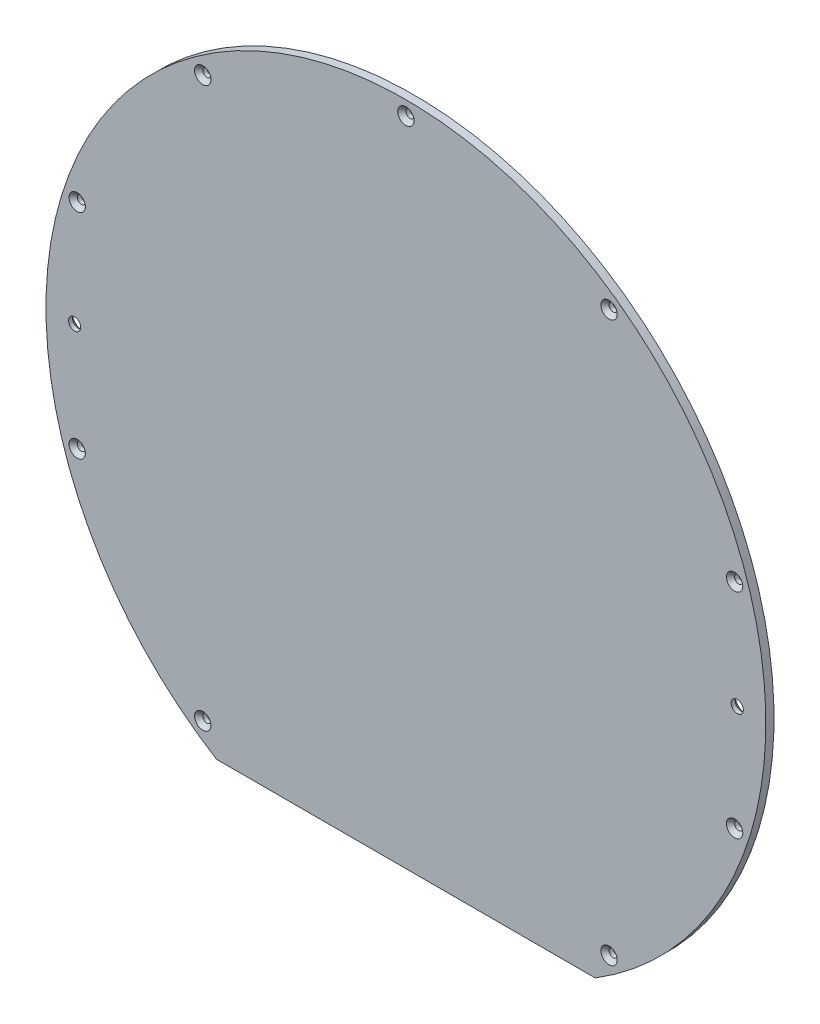
SolidWorks part; units mm, degrees
ref_plane "Plano frontal" through (0, 0, 0) normal (0, 0, 1) x (1, 0, 0)
ref_plane "Plano superior" through (0, 0, 0) normal (0, 1, 0) x (1, 0, 0)
ref_plane "Plano direito" through (0, 0, 0) normal (1, 0, 0) x (0, 0, -1)
sketch "Esboço1" plane through (0, 0, 0) normal (0, 0, 1) x (1, 0, 0)
  line L0 (-46.3033, -74.8331) -> (46.3033, -74.8331)
  line L1 (0, 0) -> (0, -74.8331) construction
  line L2 (-50, -74.8331) -> (50, -74.8331) construction
  arc A0 (46.3033, -74.8331) -> (-46.3033, -74.8331) centre (0, 0) ccw
  arc A1 (50, -74.8331) -> (-50, -74.8331) centre (0, 0) ccw construction
  dimension "D1" = 88
  dimension "D3" = 180
  dimension "D4" = 100
extrude "Ressalto-extrusão1" add sketch "Esboço1" along normal blind 2
sketch "Esboço3" plane through (0, 0, 2) normal (0, 0, 1) x (1, 0, 0)
  line L0 (-81, 0) -> (81, 0) construction
  circle A0 centre (81, 0) radius 1.5
  circle A1 centre (-81, 0) radius 1.5
  dimension "D1" = 3
  dimension "D2" = 162
extrude "Corte-extrusão2" cut sketch "Esboço3" against normal up to next
chamfer "Chanfro2" distance 1 angle 45 2 edges at (82.5, 0, 0) (-79.5, 0, 0)
sketch "Esboço4" plane through (0, 0, 2) normal (0, 0, 1) x (1, 0, 0)
  circle A0 centre (-49.6679, -68.3619) radius 1 construction
  circle A1 centre (-80.3643, -26.1119) radius 1 construction
  circle A2 centre (-80.3643, 26.1119) radius 1 construction
  circle A3 centre (-49.6679, 68.3619) radius 1 construction
  circle A4 centre (0, 84.5) radius 1 construction
  circle A5 centre (49.6679, 68.3619) radius 1 construction
  circle A6 centre (80.3643, 26.1119) radius 1 construction
  circle A7 centre (80.3643, -26.1119) radius 1 construction
  circle A8 centre (49.6679, -68.3619) radius 1 construction
  circle A9 centre (-49.6679, -68.3619) radius 1
  circle A10 centre (-80.3643, -26.1119) radius 1
  circle A11 centre (-80.3643, 26.1119) radius 1
  circle A12 centre (-49.6679, 68.3619) radius 1
  circle A13 centre (0, 84.5) radius 1
  circle A14 centre (49.6679, 68.3619) radius 1
  circle A15 centre (80.3643, 26.1119) radius 1
  circle A16 centre (80.3643, -26.1119) radius 1
  circle A17 centre (49.6679, -68.3619) radius 1
extrude "Corte-extrusão3" cut sketch "Esboço4" against normal up to next
chamfer "Chanfro3" distance 1 angle 45 9 edges at (50.6679, -68.3619, 2) (81.3643, -26.1119, 2) (81.3643, 26.1119, 2) (50.6679, 68.3619, 2) (1, 84.5, 2) (-48.6679, 68.3619, 2) (-79.3643, 26.1119, 2) (-79.3643, -26.1119, 2) (-48.6679, -68.3619, 2)
